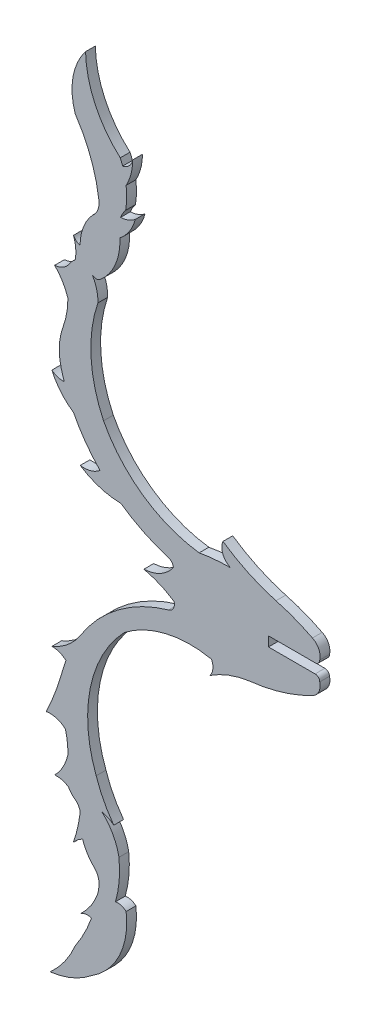
SolidWorks part; units mm, degrees
ref_plane "Front Plane" through (0, 0, 0) normal (0, 0, 1) x (1, 0, 0)
ref_plane "Top Plane" through (0, 0, 0) normal (0, 1, 0) x (1, 0, 0)
ref_plane "Right Plane" through (0, 0, 0) normal (1, 0, 0) x (0, 0, -1)
sketch "Sketch1" plane through (0, 0, 0) normal (0, 0, 1) x (1, 0, 0)
  line L55 (-277.916, 935.8846) -> (-285.2032, 935.8846)
  line L56 (-285.2032, 935.8846) -> (-285.2032, 937.391)
  line L57 (-285.2032, 937.391) -> (-277.916, 937.391)
  arc A0 (-314.5915, 922.7402) -> (-319.0227, 919.0573) centre (-322.6528, 927.9323) cw
  arc A1 (-319.0227, 919.0573) -> (-316.8191, 918.2386) centre (-318.9334, 915.923) cw
  arc A2 (-317.5377, 915.9689) -> (-319.9223, 909.7959) centre (-354.2466, 926.6019) cw
  arc A3 (-319.9223, 909.7959) -> (-316.8979, 908.9199) centre (-319.2933, 906.3086) cw
  arc A4 (-316.5214, 905.6284) -> (-318.5845, 901.8859) centre (-324.0418, 907.3343) cw
  arc A5 (-318.5845, 901.8859) -> (-316.437, 901.3374) centre (-318.2186, 898.8402) cw
  arc A6 (-314.6008, 898.8402) -> (-315.677, 894.2054) centre (-335.6398, 901.2834) cw
  arc A7 (-315.677, 894.2054) -> (-314.2274, 895.3804) centre (-312.5212, 891.7938) cw
  arc A8 (-311.8164, 889.3008) -> (-314.4447, 885.2538) centre (-321.1129, 892.4612) cw
  arc A9 (-314.4447, 885.2538) -> (-312.8322, 885.4047) centre (-313.4613, 883.4369) cw
  arc A10 (-315.3651, 880.4058) -> (-319.2933, 874.9038) centre (-329.6432, 886.4465) cw
  arc A11 (-319.2933, 874.9038) -> (-312.7281, 877.7028) centre (-320.8626, 887.6839) ccw
  arc A12 (-311.8164, 889.3008) -> (-311.716, 889.9616) centre (-334.0582, 893.0189) ccw
  arc A13 (-316.8191, 918.2386) -> (-317.5377, 915.9689) centre (-294.0957, 909.7959) ccw
  arc A14 (-308.5496, 895.7687) -> (-309.093, 889.4806) centre (-324.705, 893.9972) cw
  arc A15 (-309.093, 889.4806) -> (-307.4275, 888.9987) centre (-308.7401, 887.581) cw
  arc A16 (-312.1007, 905.0144) -> (-309.3548, 899.7082) centre (-294.3696, 910.8266) ccw
  arc A17 (-309.3548, 899.7082) -> (-311.1934, 900.5779) centre (-311.9889, 896.5178) ccw
  arc A18 (-299.9403, 934.6631) -> (-304.6476, 936.6839) centre (-307.6997, 923.0811) ccw
  arc A19 (-304.6476, 936.6839) -> (-300.0357, 939.2135) centre (-304.8901, 942.5951) ccw
  arc A20 (-308.2272, 943.7837) -> (-314.5915, 945.7474) centre (-308.1278, 955.4012) cw
  arc A21 (-314.5915, 945.7474) -> (-311.5033, 946.6094) centre (-313.9877, 949.5469) ccw
  arc A22 (-308.2272, 943.7837) -> (-300.9205, 940.2191) centre (-294.0957, 963.4797) ccw
  arc A23 (-315.6433, 952.3741) -> (-319.0227, 956.4232) centre (-310.3689, 960.211) cw
  arc A24 (-319.0227, 956.4232) -> (-317.094, 955.8174) centre (-317.3192, 958.4735) ccw
  arc A25 (-315.6433, 952.3741) -> (-311.5033, 946.6094) centre (-294.0957, 963.4797) ccw
  arc A26 (-316.5186, 967.3869) -> (-318.5845, 970.8124) centre (-324.7538, 964.7561) ccw
  arc A27 (-318.5845, 970.8124) -> (-316.437, 971.9382) centre (-318.7986, 973.832) ccw
  arc A28 (-315.381, 973.1248) -> (-315.6433, 976.3419) centre (-321.4807, 974.2467) ccw
  arc A29 (-315.6433, 976.3419) -> (-314.6194, 975.4981) centre (-314.2372, 977.005) ccw
  arc A30 (-311.8364, 969.0925) -> (-312.7236, 972.4891) centre (-317.9885, 969.2997) ccw
  arc A31 (-312.7236, 972.4891) -> (-311.4273, 972.4891) centre (-312.0754, 973.186) ccw
  arc A32 (-315.3651, 992.8698) -> (-313.7667, 1002.114) centre (-305.9966, 996.0102) cw
  arc A33 (-313.7667, 1002.114) -> (-308.3428, 990.4701) centre (-297.6815, 1002.5216) ccw
  arc A34 (-308.4235, 979.5937) -> (-305.9966, 983.314) centre (-312.6509, 985.0033) ccw
  arc A35 (-305.9966, 983.314) -> (-308.2961, 982.4342) centre (-308.4325, 986.2359) cw
  arc A36 (-307.4296, 987.1947) -> (-306.4043, 991.1575) centre (-314.5681, 991.1556) ccw
  arc A37 (-306.4043, 991.1575) -> (-307.9738, 989.5322) centre (-308.3707, 991.486) cw
  arc A38 (-307.9738, 989.5322) -> (-308.3428, 990.4701) centre (-319.0227, 985.7274) ccw
  arc A39 (-284.0276, 942.7206) -> (-292.3068, 946.6094) centre (-276.4612, 969.5872) cw
  arc A40 (-292.3068, 946.6094) -> (-291.1176, 943.6381) centre (-290.1937, 945.7315) ccw
  arc A41 (-288.1977, 929.791) -> (-294.3696, 927.4467) centre (-286.0479, 914.8341) ccw
  arc A42 (-294.3696, 927.4467) -> (-294.1149, 929.7992) centre (-295.9691, 928.8099) ccw
  arc A43 (-288.1977, 929.791) -> (-278.334, 932.7445) centre (-291.1176, 957.4896) ccw
  arc A44 (-291.1176, 943.6381) -> (-296.0267, 943.2021) centre (-291.1176, 915.786) ccw
  arc A137 (-311.716, 889.9616) -> (-312.68, 892.7344) centre (-314.4447, 890.5669) ccw
  arc A138 (-315.3651, 880.4058) -> (-312.8322, 885.4047) centre (-334.0582, 893.0189) ccw
  arc A140 (-312.7281, 877.7028) -> (-307.4275, 888.9987) centre (-319.0227, 887.5482) ccw
  arc A142 (-308.5496, 895.7687) -> (-311.1934, 900.5779) centre (-317.0893, 894.2054) ccw
  arc A144 (-307.6997, 926.6019) -> (-312.1007, 905.0144) centre (-292.8019, 912.3224) ccw
  arc A145 (-296.0267, 930.0735) -> (-307.6997, 926.6019) centre (-297.334, 913.1085) ccw
  arc A146 (-296.0267, 930.0735) -> (-294.1149, 929.7992) centre (-291.1176, 957.4896) ccw
  arc A147 (-278.334, 932.7445) -> (-277.1929, 935.1615) centre (-279.2683, 934.6634) ccw
  arc A148 (-277.1929, 935.1615) -> (-277.916, 935.8846) centre (-277.916, 935.1615) ccw
  arc A149 (-277.916, 937.391) -> (-277.1929, 938.1141) centre (-277.916, 938.1141) ccw
  arc A150 (-277.1929, 938.1141) -> (-278.334, 940.5311) centre (-279.2683, 938.6122) ccw
  arc A151 (-278.334, 940.5311) -> (-284.0276, 942.7206) centre (-291.1176, 915.786) ccw
  arc A152 (-310.9589, 953.5971) -> (-296.0267, 943.2021) centre (-293.5128, 962.7358) ccw
  arc A153 (-311.8364, 969.0925) -> (-310.9589, 953.5971) centre (-292.3068, 962.4259) ccw
  arc A155 (-311.4273, 972.4891) -> (-308.4235, 979.5937) centre (-317.0893, 979.0702) ccw
  arc A156 (-307.498, 983.7951) -> (-308.2961, 982.4342) centre (-303.9807, 980.8176) ccw
  arc A157 (-307.498, 983.7951) -> (-307.4296, 987.1947) centre (-319.0227, 985.7274) ccw
  arc A159 (-311.716, 983.314) -> (-315.3651, 992.8698) centre (-334.0582, 980.2568) ccw
  arc A160 (-312.68, 980.5412) -> (-311.716, 983.314) centre (-314.4447, 982.7087) ccw
  arc A161 (-312.68, 980.5412) -> (-314.6194, 975.4981) centre (-307.0926, 975.4981) ccw
  arc A163 (-315.381, 973.1248) -> (-316.437, 971.9382) centre (-313.2103, 970.1298) ccw
  arc A164 (-317.2752, 963.1392) -> (-316.5186, 967.3869) centre (-328.8202, 967.3869) ccw
  arc A165 (-317.2752, 963.1392) -> (-317.5588, 957.3872) centre (-308.2272, 959.8103) ccw
  arc A166 (-317.5588, 957.3872) -> (-317.094, 955.8174) centre (-294.0957, 963.4797) ccw
  arc A167 (-300.0357, 939.2135) -> (-300.9205, 940.2191) centre (-301.2734, 939.0165) ccw
  arc A169 (-300.7931, 933.0935) -> (-299.9403, 934.6631) centre (-301.1393, 934.2981) ccw
  arc A170 (-300.7931, 933.0935) -> (-314.5915, 922.7402) centre (-294.0957, 909.7959) ccw
  arc A172 (-316.5214, 905.6284) -> (-316.8979, 908.9199) centre (-328.8202, 905.8887) ccw
  arc A173 (-316.437, 901.3374) -> (-315.381, 900.1508) centre (-313.2103, 903.1458) ccw
  arc A174 (-314.6008, 898.8402) -> (-315.381, 900.1508) centre (-316.5126, 898.5896) ccw
  arc A175 (-314.2274, 895.3804) -> (-312.68, 892.7344) centre (-307.0926, 897.7775) ccw
extrude "Boss-Extrude1" add sketch "Sketch1" along normal blind 1.524
